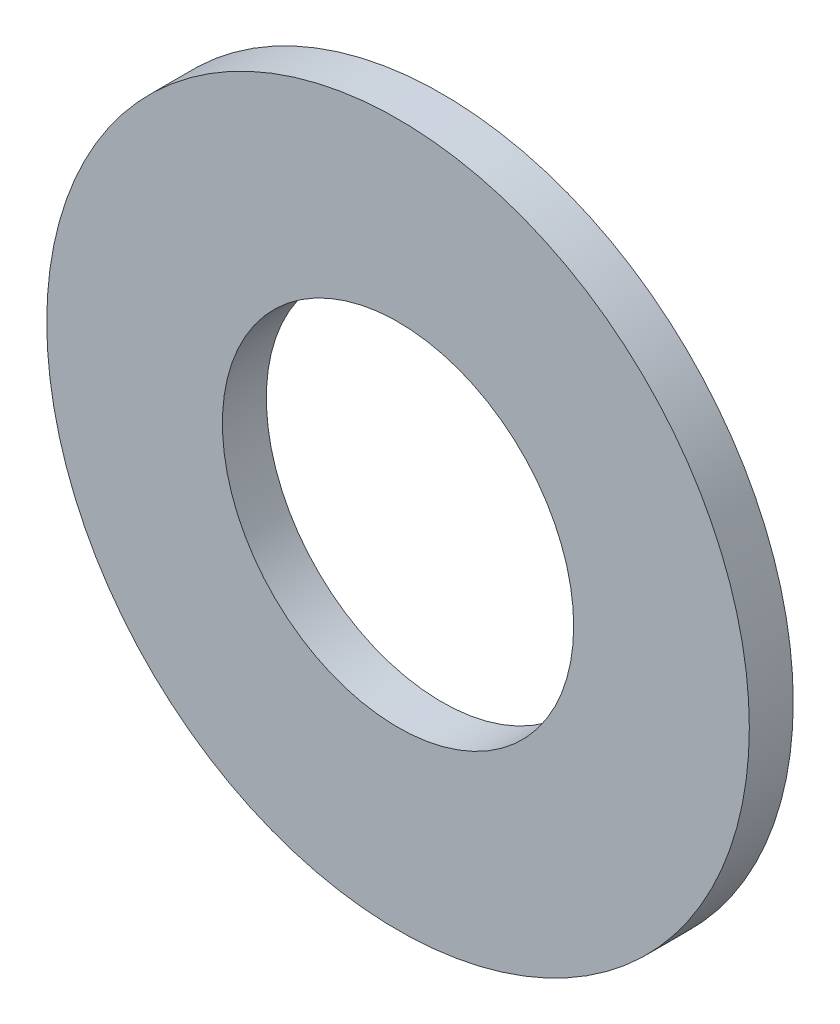
SolidWorks part; units mm, degrees
ref_plane "Front Plane" through (0, 0, 0) normal (0, 0, 1) x (1, 0, 0)
ref_plane "Top Plane" through (0, 0, 0) normal (0, 1, 0) x (1, 0, 0)
ref_plane "Right Plane" through (0, 0, 0) normal (1, 0, 0) x (0, 0, -1)
sketch "Sketch1" plane through (0, 0, 0) normal (0, 0, 1) x (1, 0, 0)
  circle A0 centre (0, 0) radius 4
  circle A1 centre (0, 0) radius 8
  dimension "D1" = 8
  dimension "D2" = 4
extrude "Boss-Extrude1" add sketch "Sketch1" along normal blind 1
